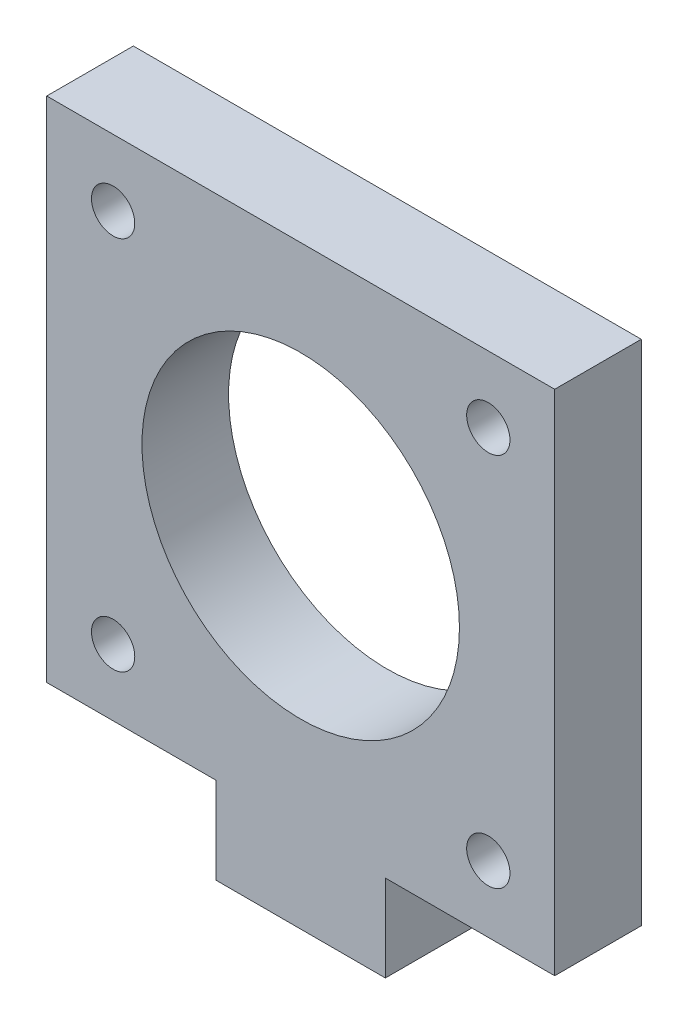
SolidWorks part; units mm, degrees
ref_plane "Front" through (0, 0, 0) normal (0, 0, 1) x (1, 0, 0)
ref_plane "Top" through (0, 0, 0) normal (0, 1, 0) x (1, 0, 0)
ref_plane "Right" through (0, 0, 0) normal (1, 0, 0) x (0, 0, -1)
sketch "Sketch1" plane through (0, 0, 0) normal (0, 0, 1) x (1, 0, 0)
  line L0 (342.9169, 225.7985) -> (342.9169, 260.9985)
  line L1 (342.9169, 260.9985) -> (307.7169, 260.9985)
  line L2 (307.7169, 260.9985) -> (307.7169, 225.7985)
  line L4 (307.7169, 225.7985) -> (319.4503, 225.7985)
  line L5 (319.4503, 225.7985) -> (319.4503, 219.7985)
  line L7 (319.4503, 219.7985) -> (331.1836, 219.7985)
  line L8 (331.1836, 219.7985) -> (331.1836, 225.7985)
  line L9 (331.1836, 225.7985) -> (342.9169, 225.7985)
  circle A0 centre (338.3169, 230.3985) radius 1.5
  circle A1 centre (338.3169, 256.3985) radius 1.5
  circle A2 centre (312.3169, 256.3985) radius 1.5
  circle A3 centre (312.3169, 230.3985) radius 1.4996
  circle A4 centre (325.3169, 243.3985) radius 11
  dimension "D1" = 35.2
  dimension "D2" = 11.7333
  dimension "D3" = 11.7333
extrude "Boss-Extrude1" add sketch "Sketch1" along normal blind 6
